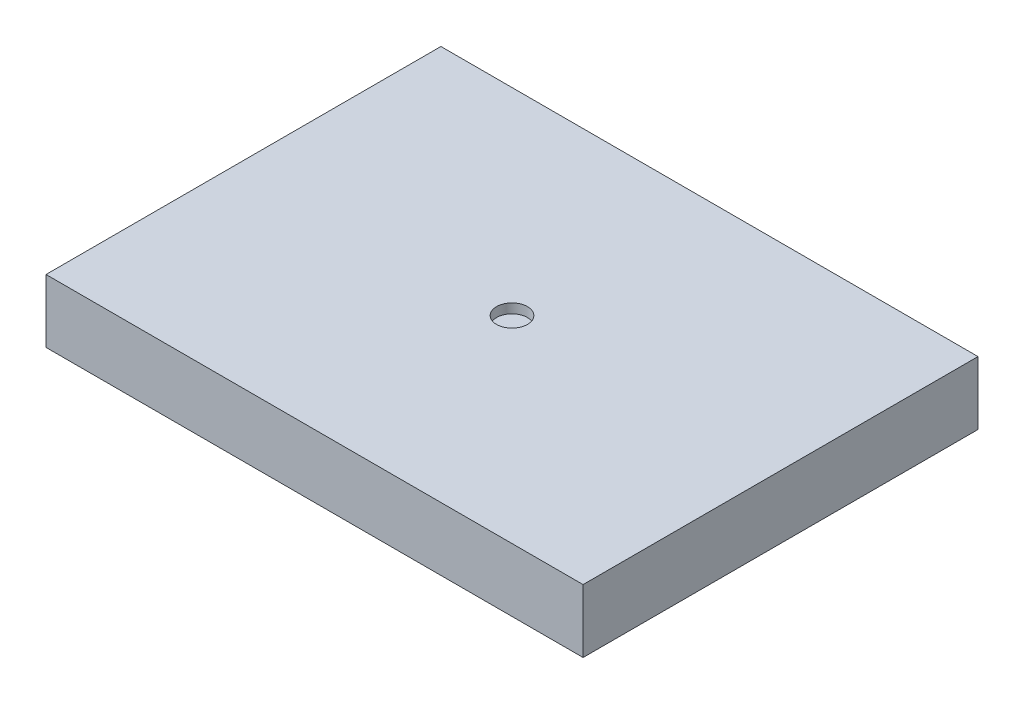
SolidWorks part; units mm, degrees
ref_plane "Front Plane" through (0, 0, 0) normal (0, 0, 1) x (1, 0, 0)
ref_plane "Top Plane" through (0, 0, 0) normal (0, 1, 0) x (1, 0, 0)
ref_plane "Right Plane" through (0, 0, 0) normal (1, 0, 0) x (0, 0, -1)
sketch "Sketch1" plane through (0, 0, 0) normal (0, 1, 0) x (1, 0, 0)
  line L1 (-21.59, 15.875) -> (21.59, 15.875)
  line L2 (-21.59, 15.875) -> (-21.59, -15.875)
  line L3 (-21.59, -15.875) -> (21.59, -15.875)
  line L4 (21.59, 15.875) -> (21.59, -15.875)
  line L5 (-21.59, 15.875) -> (21.59, -15.875) construction
  line L6 (-21.59, -15.875) -> (21.59, 15.875) construction
  point P0 (0, 0)
  dimension "D1" = 31.75
  dimension "D2" = 43.18
extrude "Boss-Extrude1" add sketch "Sketch1" along normal blind 5.08
sketch "Sketch2" plane through (0, 5.08, 0) normal (0, 1, 0) x (1, 0, 0)
  circle A0 centre (0, 0) radius 1.242
extrude "Cut-Extrude1" cut sketch "Sketch2" against normal blind 0.762
